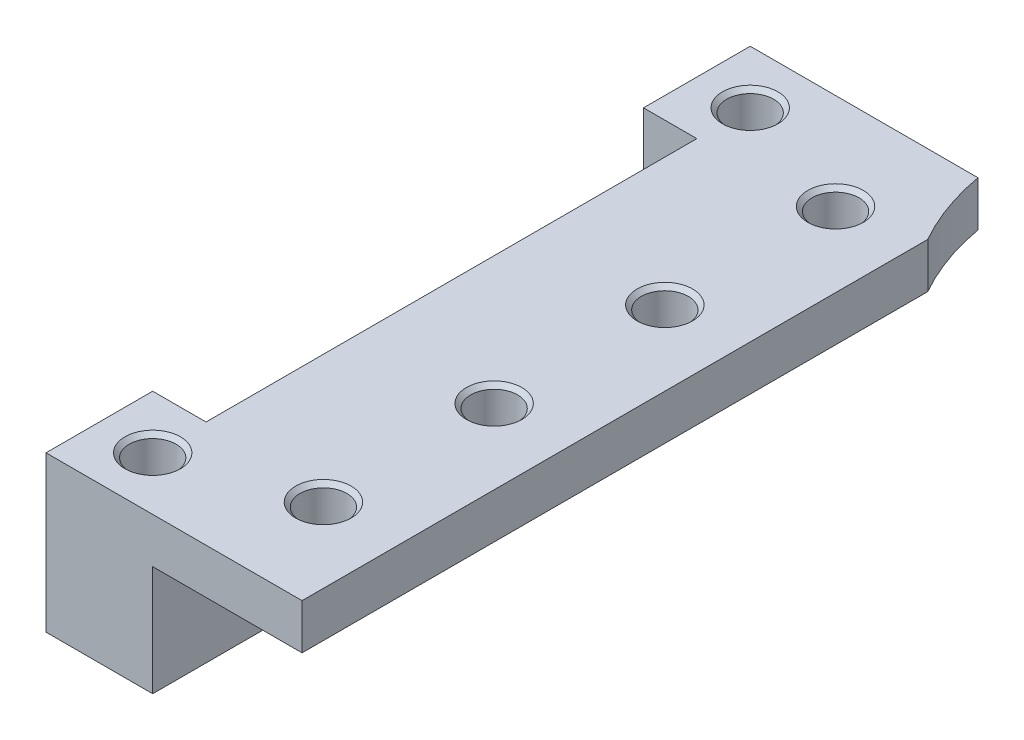
SolidWorks part; units mm, degrees
material "ABS"
ref_plane "Ön Düzlem" through (0, 0, 0) normal (0, 0, 1) x (1, 0, 0)
ref_plane "Üst Düzlem" through (0, 0, 0) normal (0, 1, 0) x (1, 0, 0)
ref_plane "Sağ Düzlem" through (0, 0, 0) normal (1, 0, 0) x (0, 0, -1)
sketch "Çizim3" plane through (0, 0, 0) normal (0, 1, 0) x (1, 0, 0)
  line L0 (16, 11.5) -> (19.5, 11.5)
  line L1 (-16, 25) -> (16, 25)
  line L2 (-16, 25) -> (-16, -25)
  line L3 (-16, -25) -> (16, -25)
  line L4 (16, 25) -> (16, -25)
  line L5 (-16, 25) -> (16, -25) construction
  line L6 (-16, -25) -> (16, 25) construction
  line L7 (16, -21.5) -> (10, -21.5)
  line L8 (16, -21.5) -> (16, 11.5)
  line L9 (16, 11.5) -> (10, 11.5)
  line L10 (10, -21.5) -> (10, 11.5)
  line L11 (19.5, 11.5) -> (19.5, -21.5)
  line L12 (19.5, -21.5) -> (16, -21.5)
  line L14 (16, 11.5) -> (22, 11.5)
  line L15 (16, 11.5) -> (16, 6.5)
  line L16 (16, 6.5) -> (22, 6.5)
  line L17 (22, 11.5) -> (22, 6.5)
  line L18 (16, -21.5) -> (22, -21.5)
  line L19 (16, -21.5) -> (16, -16.5)
  line L20 (16, -16.5) -> (22, -16.5)
  line L21 (22, -21.5) -> (22, -16.5)
  line L22 (16, 6.5) -> (19.5, 6.5)
  line L23 (16, 6.5) -> (16, -16.5)
  line L24 (16, -16.5) -> (19.5, -16.5)
  line L25 (19.5, 6.5) -> (19.5, -16.5)
  circle A0 centre (0, 13.5) radius 11
  circle A1 centre (0, 13.5) radius 11.5
  point P0 (0, 0)
  dimension "D3" = 22
  dimension "D8" = 23
  dimension "D1" = 32
  dimension "D2" = 50
  dimension "D4" = 11.5
  dimension "D5" = 6
  dimension "D6" = 13.5
  dimension "D7" = 33
  dimension "D9" = 3.5
  dimension "D10" = 6
  dimension "D11" = 5
  dimension "D12" = 5
  dimension "D13" = 6
  dimension "D14" = 3.5
extrude "Yükseklik-Ekstrüzyon3" add sketch "Çizim3" along normal blind 8.28 contours A1 L10 L7 L4 L8 L9 | L8 L20 L11 L16 | L4 L16 L11 L0 | L17 L14 L11 L16 | L20 L4 L12 L11 | L18 L21 L20 L11
sketch "Çizim4" plane through (0, 0, 21.5) normal (0, 0, 1) x (1, 0, 0)
  line L1 (10, 0) -> (17, 0)
  line L2 (10, 0) -> (10, 5.16)
  line L3 (10, 5.16) -> (17, 5.16)
  line L4 (17, 0) -> (17, 5.16)
  dimension "D1" = 5.16
  dimension "D2" = 7
extrude "Kes-Ekstrüzyon1" cut sketch "Çizim4" against normal through all
sketch "Vida Deliği Ref." plane through (0, 8.28, 0) normal (0, 1, 0) x (1, 0, 0)
  line L0 (19.5, 6.5) -> (19.5, -16.5) construction
  line L1 (22, 11.5) -> (11.3248, 11.5) construction
  line L2 (22, 11.5) -> (22, 6.5) construction
  line L3 (22, -21.5) -> (22, -16.5) construction
  line L4 (22, -21.5) -> (10, -21.5) construction
  point P0 (13.5, 7)
  point P1 (13.5, -1)
  point P2 (13.5, -9)
  point P3 (13.5, -17)
  point P8 (19.5, 9)
  point P9 (19.5, -19)
  dimension "D1" = 6
  dimension "D2" = 4.5
  dimension "D3" = 8
  dimension "D4" = 8
  dimension "D5" = 8
  dimension "D6" = 2.5
  dimension "D7" = 2.5
  dimension "D8" = 2.5
  dimension "D9" = 2.5
sketch "Çizim11" plane through (0, 8.28, 0) normal (0, 1, 0) x (1, 0, 0)
  line L0 (22, 11.5) -> (11.3248, 11.5) construction
  line L9 (22, -21.5) -> (10, -21.5)
  line L10 (22, -21.5) -> (22, 11.5)
  line L11 (22, 11.5) -> (10, 11.5)
  line L12 (10, -21.5) -> (10, 11.5)
  dimension "D1" = 12
extrude "Kes-Ekstrüzyon2" cut sketch "Çizim11" against normal blind 1
sketch "Vida Deliği Ref_2" plane through (0, 7.28, 0) normal (0, 1, 0) x (1, 0, 0)
  point P0 (13.5, 7)
  point P1 (19.5, -19)
  point P2 (19.5, 9)
  point P4 (13.5, -1)
  point P7 (13.5, -9)
  point P9 (13.5, -17)
hole_wizard "M2 Düz Başlı Makine Vidası İçin Havşa_ DEĞİŞTİREBİLİRİZ" positions "3B Çizim8" profile "Çizim15" countersink size "M2" standard "ANSI Metrik" end condition through all
sketch3d "3B Çizim8"
  point P0 (19.5, 7.28, 19)
  point P3 (19.5, 7.28, -9)
  point P6 (13.5, 7.28, 17)
  point P9 (13.5, 7.28, 9)
  point P12 (13.5, 7.28, 1)
  point P15 (13.5, 7.28, -7)
sketch "Çizim15" plane through (19.5, 7.28, 19) normal (1, 0, 0) x (0, 0, 1)
  line L0 (0, 0) -> (0, 7.28)
  line L1 (0, 7.28) -> (1.1, 7.28)
  line L2 (1.1, 7.28) -> (1.1, 0.2)
  line L3 (1.1, 0.2) -> (1.3, 0)
  line L5 (1.3, 0) -> (0, 0)
  line L6 (-1.1, 0.2) -> (-1.3, 0) construction
  line L11 (0, -6.35) -> (0, 107.95) construction
  dimension "Thru Hole Dia." = 2.2
  dimension "Thru Hole Depth" = 7.28
  dimension "Near C'Sink Dia." = 2.6
  dimension "Near C'Sink Angle" = 90
mirror "Aynalama2" about plane through (10, 8.28, 0) normal (-1, 0, 0) of "Yükseklik-Ekstrüzyon3", "M2 Düz Başlı Makine Vidası İçin Havşa_ DEĞİŞTİREBİLİRİZ", "Kes-Ekstrüzyon2", "Kes-Ekstrüzyon1"
sketch "Çizim16" plane through (0, 7.28, 0) normal (0, 1, 0) x (1, 0, 0)
  line L1 (22, -21.5) -> (10, -21.5)
  line L2 (22, -21.5) -> (22, 11.5)
  line L3 (22, 11.5) -> (10, 11.5)
  line L4 (10, -21.5) -> (10, 11.5)
  dimension "D1" = 12
  dimension "D2" = 33
extrude "Kes-Ekstrüzyon3" cut sketch "Çizim16" against normal blind 10
